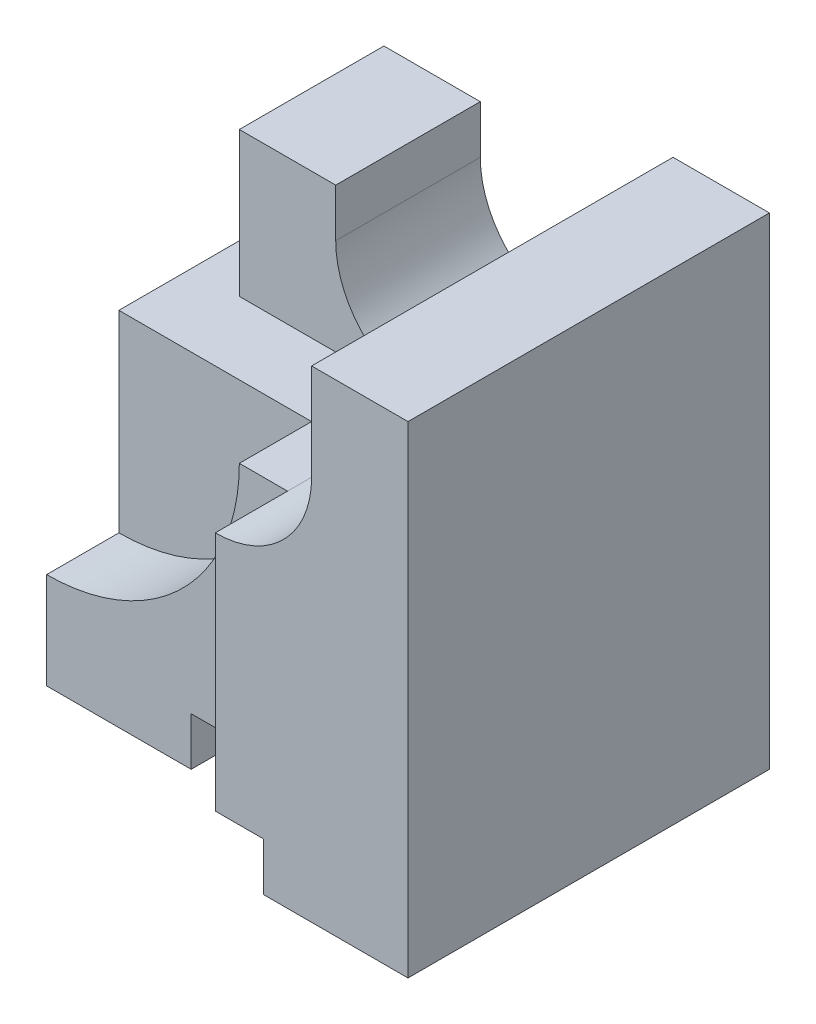
SolidWorks part; units mm, degrees
ref_plane "Front" through (0, 0, 0) normal (0, 0, 1) x (1, 0, 0)
ref_plane "Top" through (0, 0, 0) normal (0, 1, 0) x (1, 0, 0)
ref_plane "Right" through (0, 0, 0) normal (1, 0, 0) x (0, 0, -1)
sketch "Sketch1" plane through (0, 0, 0) normal (0, 0, 1) x (1, 0, 0)
  line L0 (5, 11.4338) -> (5, 8) construction
  line L1 (0, 0) -> (9, 0)
  line L2 (0, 0) -> (0, 6)
  line L3 (7, 10) -> (9, 10)
  line L4 (9, 0) -> (9, 10)
  line L5 (3, 0) -> (6, 0)
  line L6 (3, 0) -> (3, 1)
  line L7 (3, 1) -> (6, 1)
  line L8 (6, 0) -> (6, 1)
  line L9 (7, 10) -> (7, 8)
  line L10 (3, 9) -> (3, 8)
  line L14 (3, 9) -> (1, 9)
  line L18 (0, 6) -> (1, 6)
  line L19 (1, 9) -> (1, 6)
  arc A1 (3, 8) -> (7, 8) centre (5, 8) ccw
  point P11 (4.3944, 9)
  point P17 (5, 6.7709)
  point P19 (5, 7.1607)
  dimension "D7" = 2
  dimension "D1" = 9
  dimension "D2" = 10
  dimension "D3" = 3
  dimension "D4" = 1
  dimension "D5" = 3
  dimension "D6" = 2
  dimension "D8" = 1
  dimension "D9" = 3
  dimension "D10" = 4
  dimension "D11" = 180
  dimension "D12" = 3.4338
  dimension "D13" = 1
  dimension "D14" = 2
  dimension "D15" = 2
extrude "Boss-Extrude1" add sketch "Sketch1" along normal mid plane 7.5 contours A1 L10 L14 L19 L18 L2 L1 L6 L7 L8 L4 L3 L9
sketch "Sketch2" plane through (0, 0, 3.75) normal (0, 0, 1) x (1, 0, 0)
  line L1 (1, 6) -> (5, 6)
  line L2 (1, 6) -> (1, 10.1007)
  line L3 (1, 10.1007) -> (5, 10.1007)
  line L4 (5, 6) -> (5, 10.1007)
  dimension "D1" = 4
extrude "Cut-Extrude1" cut sketch "Sketch2" against normal blind 4.5 contours L3 L4 L1 L2
sketch "Sketch3" plane through (0, 0, 3.75) normal (0, 0, 1) x (1, 0, 0)
  line L1 (0, 0) -> (5, 0)
  line L2 (0, 0) -> (0, 9.9394)
  line L3 (0, 9.9394) -> (5, 9.9394)
  line L4 (5, 0) -> (5, 9.9394)
  dimension "D1" = 5
extrude "Cut-Extrude2" cut sketch "Sketch3" against normal blind 1.5
sketch "Sketch4" plane through (0, 0, 2.25) normal (0, 0, 1) x (1, 0, 0)
  line L0 (1, 6) -> (5, 6) construction
  line L1 (0, 6) -> (0, 0) construction
  line L2 (4, 6) -> (0, 6)
  line L3 (0, 6) -> (0, 2)
  arc A0 (4, 6) -> (0, 2) centre (0, 6) cw
  point P9 (0.1445, 2.0026)
  dimension "D3" = 4
  dimension "D1" = 4
  dimension "D2" = 4
extrude "Cut-Extrude3" cut sketch "Sketch4" against normal blind 1.5
